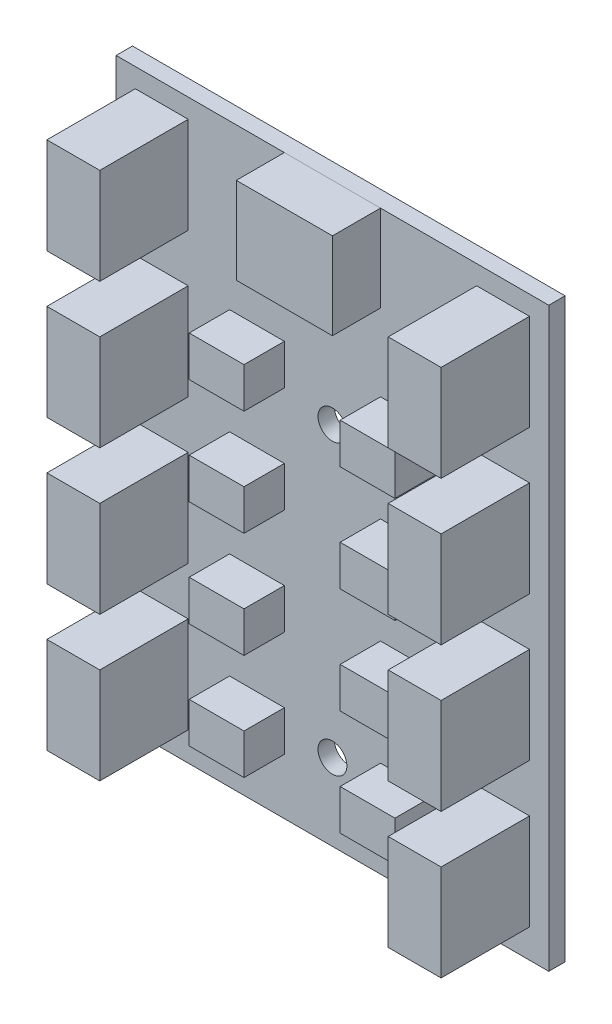
SolidWorks part; units mm, degrees
ref_plane "前视基准面" through (0, 0, 0) normal (0, 0, 1) x (1, 0, 0)
ref_plane "上视基准面" through (0, 0, 0) normal (0, 1, 0) x (1, 0, 0)
ref_plane "右视基准面" through (0, 0, 0) normal (1, 0, 0) x (0, 0, -1)
sketch "草图1" plane through (0, 0, 0) normal (0, 0, 1) x (1, 0, 0)
  line L1 (-22.5, -30) -> (22.5, -30)
  line L2 (-22.5, -30) -> (-22.5, 30)
  line L3 (-22.5, 30) -> (22.5, 30)
  line L4 (22.5, -30) -> (22.5, 30)
  line L5 (0, 30) -> (0, -30) construction
  line L6 (-22.5, 0) -> (22.5, 0) construction
  circle A0 centre (0, -22) radius 1.5
  circle A1 centre (0, 8) radius 1.5
  point P0 (0, 0)
  dimension "D5" = 3
  dimension "D1" = 45
  dimension "D2" = 60
  dimension "D3" = 8
  dimension "D4" = 30
extrude "板厚" add sketch "草图1" along normal blind 1.7
sketch "草图2" plane through (0, 0, 1.7) normal (0, 0, 1) x (1, 0, 0)
  line L0 (22.5, 30) -> (-22.5, 30) construction
  line L1 (-5, 30) -> (5, 30)
  line L2 (-5, 30) -> (-5, 21)
  line L3 (-5, 21) -> (5, 21)
  line L4 (5, 30) -> (5, 21)
  line L5 (0, 0) -> (0, 30) construction
  dimension "D1" = 10
  dimension "D2" = 9
extrude "侧向xt30" add sketch "草图2" along normal blind 5 separate body
sketch "草图3" plane through (0, 0, 1.7) normal (0, 0, 1) x (1, 0, 0)
  line L0 (22.5, 30) -> (-22.5, 30) construction
  line L1 (-20.5, 28) -> (-15, 28)
  line L2 (-20.5, 28) -> (-20.5, 18)
  line L3 (-20.5, 18) -> (-15, 18)
  line L4 (-15, 28) -> (-15, 18)
  line L5 (-22.5, 30) -> (-22.5, -30) construction
  line L6 (-20.5, 13) -> (-20.5, 3)
  line L7 (-20.5, 13) -> (-15, 13)
  line L8 (-15, 13) -> (-15, 3)
  line L9 (-20.5, 3) -> (-15, 3)
  line L10 (-20.5, -2) -> (-20.5, -12)
  line L11 (-20.5, -2) -> (-15, -2)
  line L12 (-15, -2) -> (-15, -12)
  line L13 (-20.5, -12) -> (-15, -12)
  line L14 (-20.5, -17) -> (-20.5, -27)
  line L15 (-20.5, -17) -> (-15, -17)
  line L16 (-15, -17) -> (-15, -27)
  line L17 (-20.5, -27) -> (-15, -27)
  line L18 (-20.5, 28) -> (-20.5, 13) construction
  line L19 (0, 0) -> (0, -17) construction
  line L20 (20.5, 28) -> (20.5, 13) construction
  line L21 (20.5, -27) -> (15, -27)
  line L22 (15, -17) -> (15, -27)
  line L23 (20.5, -17) -> (15, -17)
  line L24 (20.5, -17) -> (20.5, -27)
  line L25 (20.5, -12) -> (15, -12)
  line L26 (15, -2) -> (15, -12)
  line L27 (20.5, -2) -> (15, -2)
  line L28 (20.5, -2) -> (20.5, -12)
  line L29 (20.5, 3) -> (15, 3)
  line L30 (15, 13) -> (15, 3)
  line L31 (20.5, 13) -> (15, 13)
  line L32 (20.5, 13) -> (20.5, 3)
  line L33 (15, 28) -> (15, 18)
  line L34 (20.5, 18) -> (15, 18)
  line L35 (20.5, 28) -> (20.5, 18)
  line L36 (15, 28) -> (20.5, 28)
  dimension "D1" = 2
  dimension "D2" = 2
  dimension "D3" = 10
  dimension "D4" = 5.5
  dimension "D6" = 15
  dimension "D5" = 4
extrude "法相xt30" add sketch "草图3" along normal blind 9.2 separate body
sketch "草图4" plane through (0, 0, 1.7) normal (0, 0, 1) x (1, 0, 0)
  line L0 (-15, 13) -> (-20.5, 13) construction
  line L1 (-10.7, 13) -> (-5, 13)
  line L2 (-10.7, 13) -> (-10.7, 8.8)
  line L3 (-10.7, 8.8) -> (-5, 8.8)
  line L4 (-5, 13) -> (-5, 8.8)
  line L5 (-15, 3) -> (-15, 13) construction
  line L6 (-10.7, 2) -> (-10.7, -2.2)
  line L7 (-10.7, 2) -> (-5, 2)
  line L8 (-5, 2) -> (-5, -2.2)
  line L9 (-10.7, -2.2) -> (-5, -2.2)
  line L10 (-10.7, -9) -> (-10.7, -13.2)
  line L11 (-10.7, -9) -> (-5, -9)
  line L12 (-5, -9) -> (-5, -13.2)
  line L13 (-10.7, -13.2) -> (-5, -13.2)
  line L14 (-10.7, -20) -> (-10.7, -24.2)
  line L15 (-10.7, -20) -> (-5, -20)
  line L16 (-5, -20) -> (-5, -24.2)
  line L17 (-10.7, -24.2) -> (-5, -24.2)
  line L18 (-10.7, 13) -> (-10.7, 2) construction
  line L19 (0, 0) -> (0, 17.9048) construction
  line L20 (10.7, 13) -> (10.7, 2) construction
  line L21 (10.7, -24.2) -> (5, -24.2)
  line L22 (5, -20) -> (5, -24.2)
  line L23 (10.7, -20) -> (5, -20)
  line L24 (10.7, -20) -> (10.7, -24.2)
  line L25 (10.7, -13.2) -> (5, -13.2)
  line L26 (5, -9) -> (5, -13.2)
  line L27 (10.7, -9) -> (5, -9)
  line L28 (10.7, -9) -> (10.7, -13.2)
  line L29 (10.7, -2.2) -> (5, -2.2)
  line L30 (5, 2) -> (5, -2.2)
  line L31 (10.7, 2) -> (5, 2)
  line L32 (10.7, 2) -> (10.7, -2.2)
  line L33 (5, 13) -> (5, 8.8)
  line L34 (10.7, 8.8) -> (5, 8.8)
  line L35 (10.7, 13) -> (10.7, 8.8)
  line L36 (10.7, 13) -> (5, 13)
  dimension "D1" = 5.7
  dimension "D2" = 4.2
  dimension "D3" = 4.3
  dimension "D5" = 11
  dimension "D4" = 4
extrude "法相can" add sketch "草图4" along normal blind 4.2 separate body
